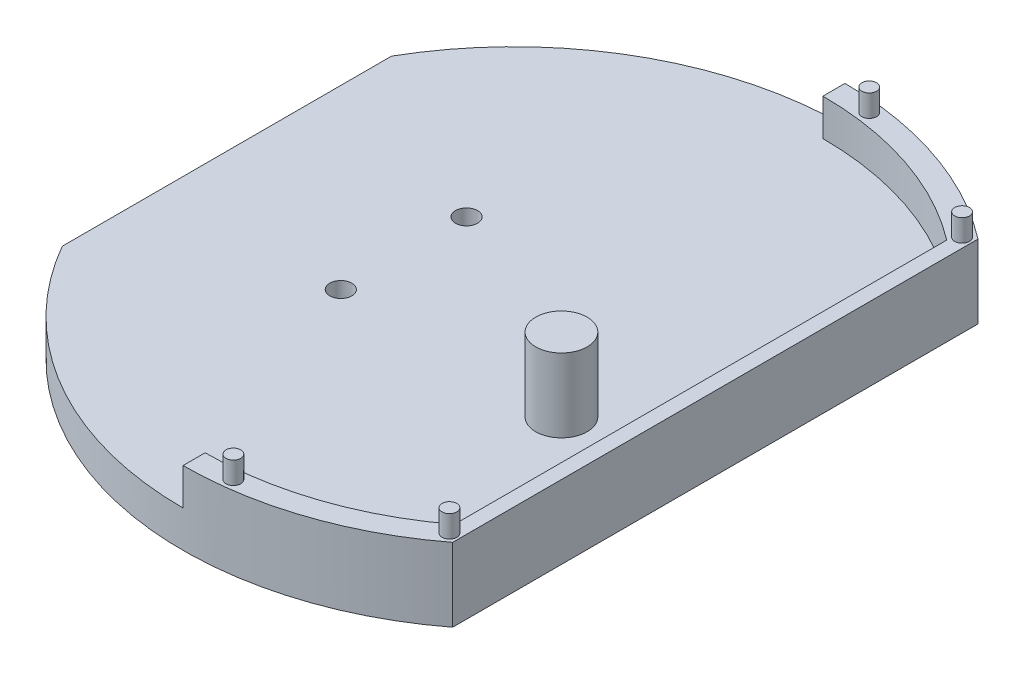
SolidWorks part; units mm, degrees
material "A-玻璃纤维"
ref_plane "前视基准面" through (0, 0, 0) normal (0, 0, 1) x (1, 0, 0)
ref_plane "上视基准面" through (0, 0, 0) normal (0, 1, 0) x (1, 0, 0)
ref_plane "右视基准面" through (0, 0, 0) normal (1, 0, 0) x (0, 0, -1)
sketch "草图1" plane through (0, 0, 0) normal (0, 1, 0) x (1, 0, 0)
  line L0 (-39.0386, -22.3828) -> (-39.0386, 22.3828)
  line L5 (-23.181, 22.3828) -> (23.181, -22.3828) construction
  line L6 (-23.181, -22.3828) -> (23.181, 22.3828) construction
  line L7 (-15, -8.55) -> (15, -8.55)
  line L8 (-15, -8.55) -> (-15, -7.05)
  line L9 (-15, 8.55) -> (15, 8.55)
  line L10 (15, -8.55) -> (15, 8.55)
  line L11 (-15, -8.55) -> (15, 8.55) construction
  line L12 (-15, 8.55) -> (15, -8.55) construction
  line L13 (27.3745, -35.716) -> (27.3745, 35.716)
  line L14 (-15, 7.05) -> (-15, 8.55)
  circle A0 centre (-15, 8.55) radius 1.5
  circle A1 centre (-15, -8.55) radius 1.5
  circle A3 centre (15, 8.55) radius 3
  arc A4 (-39.0386, -22.3828) -> (27.3745, -35.716) centre (0, 0) ccw
  arc A5 (27.3745, 35.716) -> (-39.0386, 22.3828) centre (0, 0) ccw
  circle A6 centre (15, 8.55) radius 3
  point P0 (0, 0)
  point P6 (0, 0)
  dimension "D3" = 3
  dimension "D4" = 6
  dimension "D5" = 3
  dimension "D1" = 17.1
  dimension "D2" = 30
extrude "凸台-拉伸1" add sketch "草图1" along normal blind 5
sketch "草图2" plane through (0, 5, 0) normal (0, 1, 0) x (1, 0, 0)
  circle A1 centre (-15, 8.55) radius 1.5 construction
  circle A2 centre (15, -8.55) radius 3.5
  circle A3 centre (-15, -8.55) radius 1.5 construction
  dimension "D2" = 30
  dimension "D3" = 17.1
extrude "凸台-拉伸2" add sketch "草图2" along normal blind 10
sketch "草图3" plane through (0, 5, 0) normal (0, 1, 0) x (1, 0, 0)
  line L0 (25.3745, -37.1636) -> (25.3745, 37.1636)
  line L1 (27.3745, -35.716) -> (27.3745, 35.716) construction
  line L2 (0, -45) -> (0, 45)
  circle A0 centre (0, 0) radius 42
  arc A1 (-39.0386, -22.3828) -> (27.3745, -35.716) centre (0, 0) ccw construction
  arc A2 (27.3745, 35.716) -> (-39.0386, 22.3828) centre (0, 0) ccw construction
  circle A3 centre (0, 0) radius 45
  line M7 (27.3745, -35.716) -> (27.3745, 35.716)
  arc M8 (27.3745, 35.716) -> (-39.0386, 22.3828) centre (0, 0) ccw
  arc M10 (-39.0386, -22.3828) -> (27.3745, -35.716) centre (0, 0) ccw
  dimension "D1" = 2
extrude "凸台-拉伸3" add sketch "草图3" along normal blind 5 contours A0 L2 L0 M10 | A0 L0 M10 M7 | L0 A0 M7 | A0 L0 M7 M8 | A0 L0 L2 M8
sketch "草图4" plane through (0, 10, 0) normal (0, 1, 0) x (1, 0, 0)
  line L0 (27.3745, -35.716) -> (27.3745, 35.716) construction
  circle A0 centre (0, 0) radius 43.5238
  circle A1 centre (26.0745, -34.8488) radius 1
  circle A2 centre (5.0745, -43.227) radius 1
  circle A3 centre (26.0745, 34.8488) radius 1
  circle A4 centre (5.0745, 43.227) radius 1
  dimension "D1" = 1.3
  dimension "D2" = 22.3
  dimension "D3" = 1.3
  dimension "D4" = 22.3
extrude "凸台-拉伸4" add sketch "草图4" along normal blind 3 contours A0 A4 | A0 A4 | A0 A3 | A0 A3 | A0 A1 | A0 A1 | A0 A2 | A0 A2
